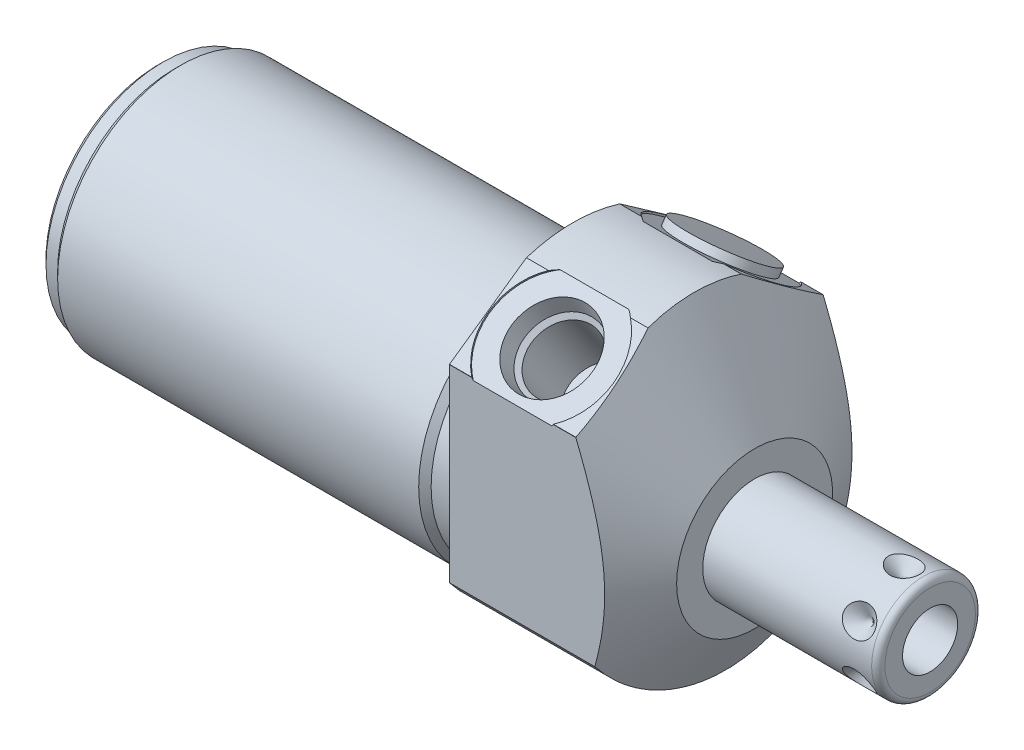
SolidWorks part; units mm, degrees
material "Alloy Steel"
ref_plane "Front Plane" through (0, 0, 0) normal (0, 0, 1) x (1, 0, 0)
ref_plane "Top Plane" through (0, 0, 0) normal (0, 1, 0) x (1, 0, 0)
ref_plane "Right Plane" through (0, 0, 0) normal (1, 0, 0) x (0, 0, -1)
ref_plane "Plane1" through (0, 0, 0) normal (1, 0, 0) x (0, 0, -1)
sketch "Sketch1" plane through (0, 0, 0) normal (1, 0, 0) x (0, 0, -1)
  circle A0 centre (0, 0) radius 23.8125
  dimension "D1" = 47.625
extrude "Extrude1" add sketch "Sketch1" along normal blind 27.7876 and the other way blind 63.5
ref_plane "Plane2" through (0, 0, 0) normal (1, 0, 0) x (0, 0, -1)
sketch "Sketch2" plane through (0, 0, 0) normal (1, 0, 0) x (0, 0, -1)
  line L0 (-20.7455, -4.191) -> (20.7455, -4.191) construction
  circle A0 centre (0, -4.191) radius 18.8595
  circle A1 centre (0, 0) radius 23.8125 construction
  circle A2 centre (0, 0) radius 23.8125
  dimension "D2" = 37.719
  dimension "D1" = 4.191
extrude "Cut-Extrude1" cut sketch "Sketch2" against normal up to next
ref_plane "Plane4" through (0, 0, 0) normal (-1, 0, 0) x (0, 0, 1)
sketch "Sketch4" plane through (0, 0, 0) normal (-1, 0, 0) x (0, 0, 1)
  line L0 (18.923, -14.4553) -> (18.923, 14.4659)
  line L1 (18.923, 14.4659) -> (0, 27.7159)
  line L2 (-18.923, -14.4553) -> (-18.923, 14.4659)
  line L3 (-18.923, 14.4659) -> (0, 27.7159)
  line L4 (0, -26.3889) -> (0, 30.2923) construction
  circle A0 centre (0, 0) radius 28.575
  circle A1 centre (0, 0) radius 23.8125 construction
  arc A3 (-18.923, -14.4553) -> (18.923, -14.4553) centre (0, 0) ccw
  dimension "D4" = 57.15
  dimension "D1" = 37.846
  dimension "D2" = 27.7159
  dimension "D3" = 55
extrude "Cut-Extrude3" cut sketch "Sketch4" against normal up to next
ref_plane "Plane6" through (0, 0, 0) normal (0, 0, 1) x (1, 0, 0)
sketch "Sketch6" plane through (0, 0, 0) normal (0, 0, 1) x (1, 0, 0)
  line L0 (4.764, 47.625) -> (27.7876, 7.747)
  line L1 (3.6128, -4.191) -> (28.9388, -4.191) construction
  line L2 (-63.5, -4.191) -> (0, -4.191) construction
  line L3 (27.7876, 7.747) -> (27.7876, 47.625)
  line L4 (27.7876, 47.625) -> (4.764, 47.625)
  line L5 (27.7876, -14.4553) -> (27.7876, 14.4553) construction
  dimension "D1" = 23.876
  dimension "D2" = 30
  dimension "D3" = 39.878
revolve "Cut-Revolve2" cut sketch "Sketch6" angle 360 about L1
ref_plane "Plane7" through (9.652, 18.3948, 12.869) normal (1, 0, 0) x (0, 0.5736, -0.8192)
sketch "S2D0002" plane through (9.652, 18.3948, 12.869) normal (1, 0, 0) x (0, 0.5736, -0.8192)
  line L0 (0, 0) -> (6.1849, 0)
  line L1 (6.1849, 0) -> (5.6423, -2.5527)
  line L2 (5.6423, -2.5527) -> (4.9784, -3.2166)
  line L3 (4.9784, -3.2166) -> (4.9784, -13.462)
  line L4 (4.9784, -13.462) -> (0, -13.462)
  line L5 (0, -13.462) -> (0, 0)
  line L6 (0, -14.1351) -> (0, 0.6731) construction
  dimension "D1" = 13.462
revolve "Cut-Revolve3" cut sketch "S2D0002" angle 360 about L6
ref_plane "Plane8" through (9.652, 18.3948, -12.869) normal (1, 0, 0) x (0, -0.5736, -0.8192)
sketch "Sketch8" plane through (9.652, 18.3948, -12.869) normal (1, 0, 0) x (0, -0.5736, -0.8192)
  line L0 (0, 0) -> (6.1849, 0)
  line L1 (6.1849, 0) -> (5.6423, -2.5527)
  line L2 (5.6423, -2.5527) -> (4.9784, -3.2166)
  line L3 (4.9784, -3.2166) -> (4.9784, -13.462)
  line L4 (4.9784, -13.462) -> (0, -13.462)
  line L5 (0, -13.462) -> (0, 0)
  line L6 (0, -14.1351) -> (0, 0.6731) construction
  dimension "D1" = 13.462
revolve "Cut-Revolve4" cut sketch "Sketch8" angle 360 about L6
sketch "Sketch18" plane through (0, 18.5976, 13.0222) normal (0, 0.8192, 0.5736) x (1, 0, 0)
  circle A0 centre (9.652, 0.0091) radius 9.525
  dimension "D1" = 19.05
extrude "Cut-Extrude4" cut sketch "Sketch18" against normal blind 0.254
sketch "Sketch19" plane through (0, 18.5976, -13.0222) normal (0, 0.8192, -0.5736) x (1, 0, 0)
  circle A0 centre (9.652, -0.0091) radius 9.525
  dimension "D1" = 19.05
extrude "Cut-Extrude5" cut sketch "Sketch19" against normal blind 0.254
ref_plane "Plane10" through (0, 0, 0) normal (0, 0, 1) x (1, 0, 0)
sketch "Sketch10" plane through (0, 0, 0) normal (0, 0, 1) x (1, 0, 0)
  line L0 (0, 14.6685) -> (0, 13.716)
  line L1 (0, 13.716) -> (-3.81, 13.716)
  line L2 (-3.81, 13.716) -> (-4.7625, 14.6685)
  line L3 (-5.0006, -4.191) -> (0.2381, -4.191) construction
  line L4 (0, 14.6685) -> (-4.7625, 14.6685)
  line L5 (-63.5, -4.191) -> (0, -4.191) construction
  line L6 (0, 14.6685) -> (-63.5, 14.6685) construction
  line L7 (0, 14.6685) -> (0, -23.0505) construction
  dimension "D1" = 35.814
  dimension "D2" = 3.81
  dimension "D3" = 45
revolve "Cut-Revolve6" cut sketch "Sketch10" angle 360 about L3
ref_plane "Plane12" through (0, 0, 0) normal (0, 0, 1) x (1, 0, 0)
sketch "Sketch12" plane through (0, 0, 0) normal (0, 0, 1) x (1, 0, 0)
  line L0 (-63.5, 14.6685) -> (-63.5, 13.716)
  line L1 (-63.5, 13.716) -> (-60.96, 13.716)
  line L2 (-60.96, 13.716) -> (-60.0075, 14.6685)
  line L3 (-63.6746, -4.191) -> (-59.8329, -4.191) construction
  line L4 (-63.5, 14.6685) -> (-60.0075, 14.6685)
  line L6 (-63.5, -4.191) -> (-4.7625, -4.191) construction
  line L7 (-4.7625, 14.6685) -> (-63.5, 14.6685) construction
  line L8 (-63.5, 14.6685) -> (-63.5, -23.0505) construction
  dimension "D1" = 35.814
  dimension "D2" = 2.54
  dimension "D3" = 45
revolve "Cut-Revolve8" cut sketch "Sketch12" angle 360 about L3
chamfer "Chamfer1" distance 0.762 angle 45 1 edges at (-63.5, -4.191, 17.907)
ref_plane "Plane13" through (0, 0, 0) normal (0, 0, 1) x (0, -1, 0)
sketch "Sketch13" plane through (0, 0, 0) normal (0, 0, 1) x (0, -1, 0)
  line L0 (4.191, 27.7876) -> (4.191, 54.6354)
  line L1 (4.191, 54.6354) -> (11.1125, 54.6354)
  line L2 (12.1285, 53.6194) -> (12.1285, 27.7876)
  line L3 (12.1285, 27.7876) -> (4.191, 27.7876)
  line L4 (4.191, 26.4452) -> (4.191, 55.9778) construction
  line L5 (4.191, -60.0075) -> (4.191, -4.7625) construction
  line L6 (16.129, 27.7876) -> (-7.747, 27.7876) construction
  line L7 (14.4553, 0) -> (-14.4553, 0) construction
  arc A0 (12.1285, 53.6194) -> (11.1125, 54.6354) centre (11.1125, 53.6194) ccw
  dimension "D2" = 1.016
  dimension "D1" = 54.6354
  dimension "D3" = 15.875
revolve "Revolve1" add sketch "Sketch13" angle 360 about L4
ref_plane "Plane14" through (54.6354, -8.4074, 0) normal (0, 0, 1) x (0, -1, 0)
sketch "S2D0001" plane through (54.6354, -8.4074, 0) normal (0, 0, 1) x (0, -1, 0)
  line L0 (0, 0) -> (0, -15.24)
  line L1 (0, -15.24) -> (-4.2164, -17.7735)
  line L2 (0, 0) -> (-4.2164, 0)
  line L3 (-4.2164, 0) -> (-4.2164, -17.7735)
  line L4 (-4.2164, -18.6621) -> (-4.2164, 0.8887) construction
  line L5 (-4.2164, -1.016) -> (-4.2164, -26.8478) construction
  line L6 (2.7051, 0) -> (-11.1379, 0) construction
  dimension "D1" = 8.4328
  dimension "D2" = 15.24
  dimension "D3" = 59
revolve "Cut-Revolve9" cut sketch "S2D0001" angle 360 about L4
ref_plane "Plane15" through (27.7876, 18.3896, -12.8765) normal (0, -0.8192, 0.5736) x (0, -0.5736, -0.8192)
sketch "Sketch15" plane through (27.7876, 18.3896, -12.8765) normal (0, -0.8192, 0.5736) x (0, -0.5736, -0.8192)
  circle A0 centre (-0.0091, -18.1356) radius 6.9469
extrude "Extrude2" add sketch "Sketch15" against normal blind 1.27
ref_plane "Plane16" through (50.673, -12.1285, 0) normal (0, 0, 1) x (-1, 0, 0)
ref_plane "Plane17" through (0, -3.1433, -1.8148) normal (0, 0.866, 0.5) x (-1, 0, 0)
sketch "Sketch16" plane through (50.673, 3.7465, 0) normal (0, 0, -1) x (-1, 0, 0)
  line L0 (0, 0) -> (2.413, 0)
  line L1 (2.413, 0) -> (0, -2.413)
  line L2 (0, 0) -> (0, -2.413)
  line L3 (0, -5.071) -> (0, 0.1207) construction
  line L4 (-3.9624, -1.016) -> (-3.9624, -14.859) construction
  line L5 (22.8854, 0) -> (-2.9464, 0) construction
  dimension "D1" = 3.9624
  dimension "D2" = 4.826
  dimension "D3" = 45
revolve "Cut-Revolve10" cut sketch "Sketch16" angle 360 about L3
pattern_circular "CirPattern1" count 6 over 360 about axis through (26.4452, -4.191, 0) along (-1, 0, 0) of "Cut-Revolve10"
